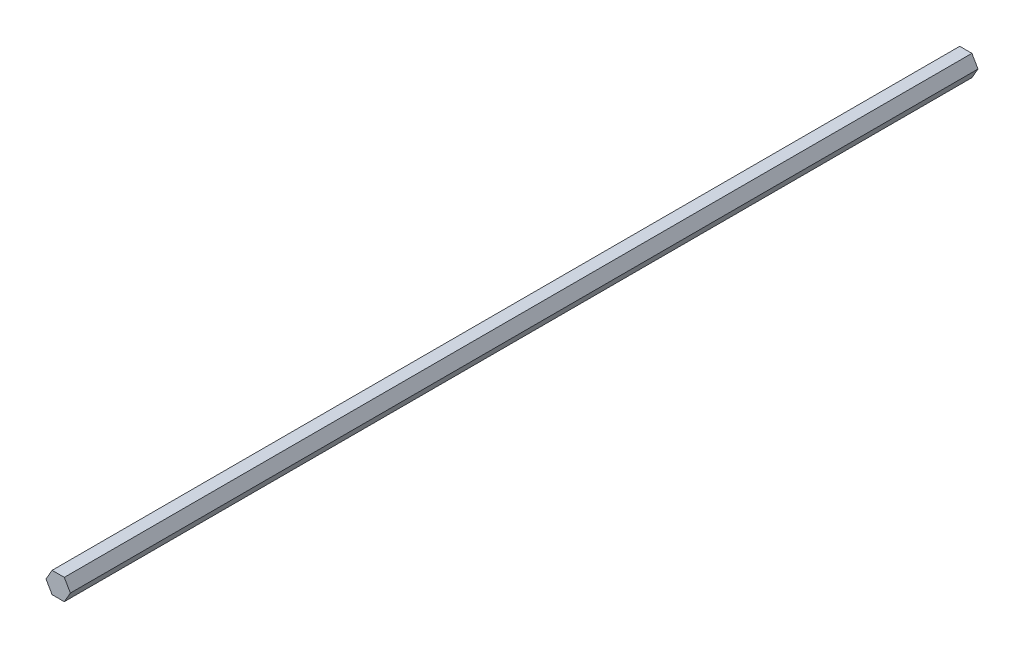
SolidWorks part; units mm, degrees
ref_plane "Front Plane" through (0, 0, 0) normal (0, 0, 1) x (1, 0, 0)
ref_plane "Top Plane" through (0, 0, 0) normal (0, 1, 0) x (1, 0, 0)
ref_plane "Right Plane" through (0, 0, 0) normal (1, 0, 0) x (0, 0, -1)
sketch "Sketch1" plane through (0, 0, 0) normal (0, 0, 1) x (1, 0, 0)
  line L1 (7.3323, 0) -> (3.6662, 6.35)
  line L2 (3.6662, 6.35) -> (-3.6662, 6.35)
  line L3 (-3.6662, 6.35) -> (-7.3323, 0)
  line L4 (-7.3323, 0) -> (-3.6662, -6.35)
  line L5 (-3.6662, -6.35) -> (3.6662, -6.35)
  line L6 (3.6662, -6.35) -> (7.3323, 0)
  circle A0 centre (0, 0) radius 6.35 construction
  dimension "D1" = 12.7
extrude "Boss-Extrude1" add sketch "Sketch1" along normal blind 508 and the other way blind 38.1
